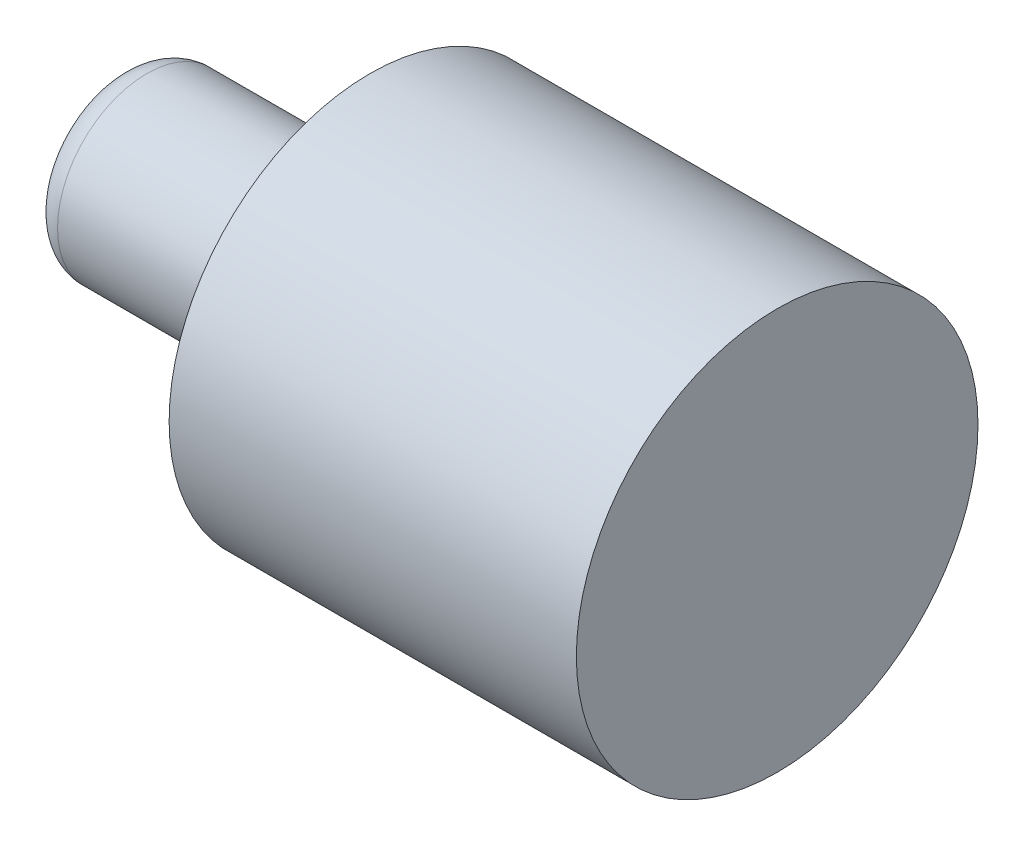
SolidWorks part; units mm, degrees
ref_plane "Front Plane" through (0, 0, 0) normal (0, 0, 1) x (1, 0, 0)
ref_plane "Top Plane" through (0, 0, 0) normal (0, 1, 0) x (1, 0, 0)
ref_plane "Right Plane" through (0, 0, 0) normal (1, 0, 0) x (0, 0, -1)
sketch "Sketch3" plane through (0, 0, 0) normal (1, 0, 0) x (0, 0, -1)
  circle A0 centre (0, 0) radius 16
extrude "Boss-Extrude1" add sketch "Sketch3" along normal blind 80
sketch "Sketch4" plane through (80, 0, 0) normal (1, 0, 0) x (0, 0, -1)
  circle A0 centre (0, 0) radius 36
extrude "Boss-Extrude2" add sketch "Sketch4" along normal blind 38
sketch "Sketch6" plane through (80, 0, 0) normal (-1, 0, 0) x (0, 0, 1)
  circle A0 centre (0, 0) radius 36
  circle A1 centre (0, 0) radius 16
extrude "Boss-Extrude3" add sketch "Sketch6" along normal blind 35
fillet "Fillet1" radius 5 2 edges at (0, 0, -16) (45, 0, 16)
